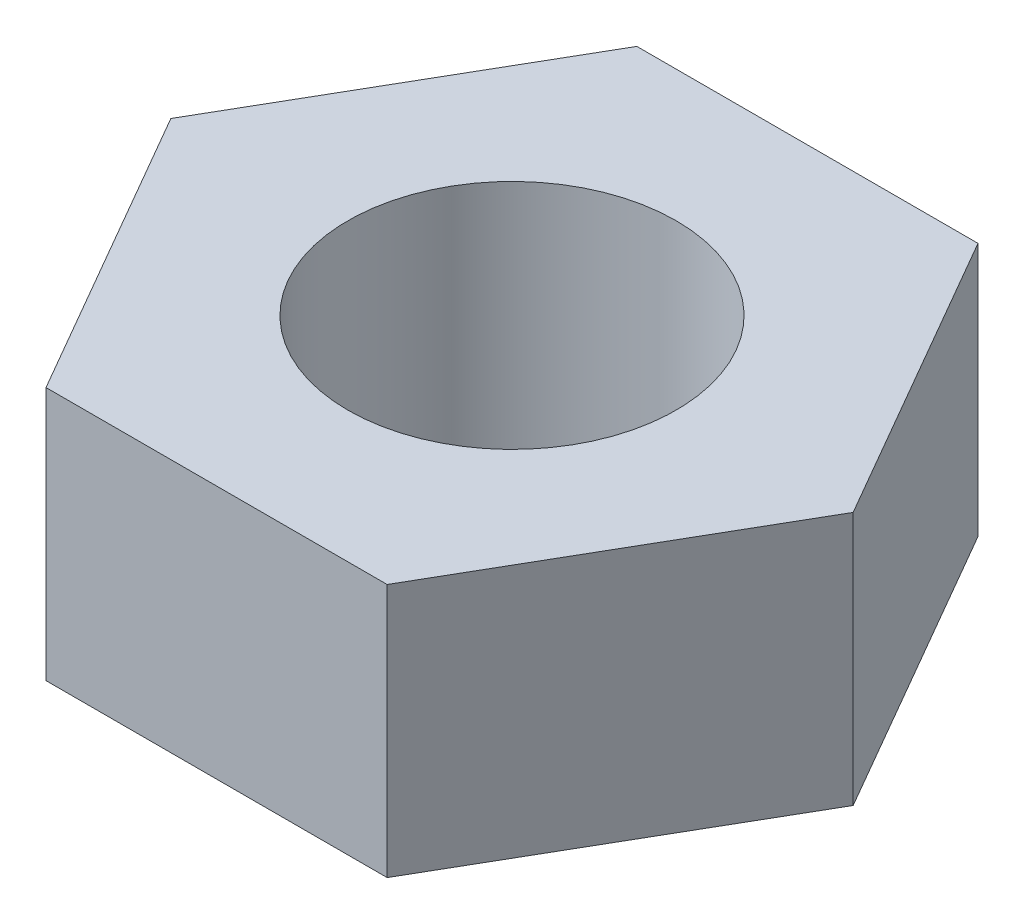
SolidWorks part; units mm, degrees
ref_plane "Front Plane" through (0, 0, 0) normal (0, 0, 1) x (1, 0, 0)
ref_plane "Top Plane" through (0, 0, 0) normal (0, 1, 0) x (1, 0, 0)
ref_plane "Right Plane" through (0, 0, 0) normal (1, 0, 0) x (0, 0, -1)
sketch "Sketch1" plane through (0, 0, 0) normal (0, 1, 0) x (1, 0, 0)
  line L1 (-1.5588, 2.7) -> (-3.1177, 0)
  line L2 (-3.1177, 0) -> (-1.5588, -2.7)
  line L3 (-1.5588, -2.7) -> (1.5588, -2.7)
  line L4 (1.5588, -2.7) -> (3.1177, 0)
  line L5 (3.1177, 0) -> (1.5588, 2.7)
  line L6 (1.5588, 2.7) -> (-1.5588, 2.7)
  circle A0 centre (0, 0) radius 2.7 construction
  circle A1 centre (0, 0) radius 1.5
  dimension "D1" = 5.4
  dimension "D2" = 3
extrude "Boss-Extrude1" add sketch "Sketch1" along normal blind 2.32
